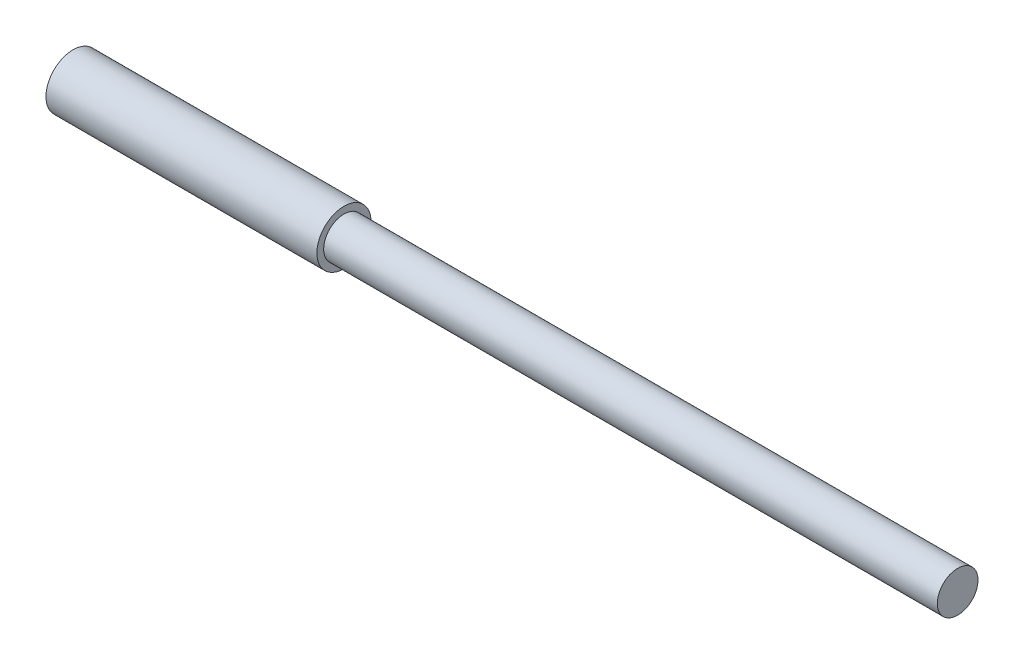
SolidWorks part; units mm, degrees
ref_plane "Face" through (0, 0, 0) normal (0, 0, 1) x (1, 0, 0)
ref_plane "Dessus" through (0, 0, 0) normal (0, 1, 0) x (1, 0, 0)
ref_plane "Droite" through (0, 0, 0) normal (1, 0, 0) x (0, 0, -1)
sketch "Esquisse1" plane through (0, 0, 0) normal (1, 0, 0) x (0, 0, -1)
  circle A0 centre (0, 0) radius 2
  dimension "D1" = 4
extrude "Extrusion1" add sketch "Esquisse1" along normal blind 20
sketch "Esquisse2" plane through (20, 0, 0) normal (1, 0, 0) x (0, 0, -1)
  circle A0 centre (0, 0) radius 1.5
  dimension "D1" = 3
extrude "Extrusion2" add sketch "Esquisse2" along normal blind 45.3
